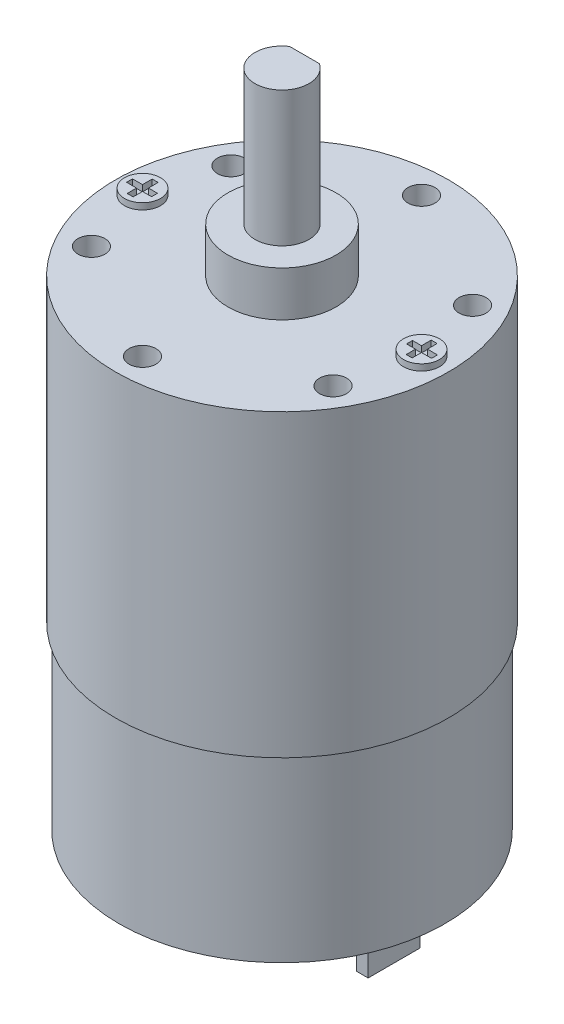
SolidWorks part; units mm, degrees
ref_plane "Front Plane" through (0, 0, 0) normal (0, 0, 1) x (1, 0, 0)
ref_plane "Top Plane" through (0, 0, 0) normal (0, 1, 0) x (1, 0, 0)
ref_plane "Right Plane" through (0, 0, 0) normal (1, 0, 0) x (0, 0, -1)
sketch "Sketch1" plane through (0, 0, 0) normal (0, 1, 0) x (1, 0, 0)
  circle A0 centre (0, 0) radius 18.1
  dimension "D1" = 36.2
extrude "Base Extrude" add sketch "Sketch1" along normal blind 20
sketch "Sketch2" plane through (0, 20, 0) normal (0, 1, 0) x (1, 0, 0)
  circle A0 centre (0, 0) radius 18.5
  dimension "D1" = 37
extrude "Motor Top" add sketch "Sketch2" along normal blind 33.3
sketch "Sketch3" plane through (0, 0, 0) normal (0, -1, 0) x (1, 0, 0)
  circle A0 centre (0, 0) radius 4.6664
extrude "Rear nub" add sketch "Sketch3" along normal blind 3.81
sketch "Sketch4" plane through (0, 0, 0) normal (0, -1, 0) x (1, 0, 0)
  line L1 (-12.7, 3.1306) -> (-11.43, 3.1306)
  line L2 (-12.7, 3.1306) -> (-12.7, -2.6581)
  line L3 (-12.7, -2.6581) -> (-11.43, -2.6581)
  line L4 (-11.43, 3.1306) -> (-11.43, -2.6581)
  line L5 (11.43, 3.1306) -> (12.7, 3.1306)
  line L6 (11.43, 3.1306) -> (11.43, -2.6581)
  line L7 (11.43, -2.6581) -> (12.7, -2.6581)
  line L8 (12.7, 3.1306) -> (12.7, -2.6581)
  dimension "D1" = 1.27
  dimension "D2" = 11.43
  dimension "D3" = 11.43
extrude "Teeth plugs" add sketch "Sketch4" along normal blind 6.35
sketch "Sketch5" plane through (0, 53.3, 0) normal (0, 1, 0) x (1, 0, 0)
  circle A0 centre (0, 0) radius 6
  dimension "D1" = 12
extrude "Axle base" add sketch "Sketch5" along normal blind 5
sketch "Sketch7" plane through (0, 58.3, 0) normal (0, 1, 0) x (1, 0, 0)
  circle A0 centre (0, 0) radius 3
  dimension "D1" = 6
extrude "Axle" add sketch "Sketch7" along normal blind 15
sketch "Sketch8" plane through (0, 0, 0) normal (1, 0, 0) x (0, 0, -1)
  line L1 (3, 73.3) -> (2.5, 73.3)
  line L2 (3, 73.3) -> (3, 59.3)
  line L3 (3, 59.3) -> (2.5, 59.3)
  line L4 (2.5, 73.3) -> (2.5, 59.3)
  point P5 (-3, 73.3)
  dimension "D1" = 5.5
  dimension "D2" = 14
extrude "D shaft cutout" cut sketch "Sketch8" against normal through all and the other way through all
sketch "Sketch9" plane through (0, 53.3, 0) normal (0, 1, 0) x (1, 0, 0)
  circle A0 centre (0, 15.5) radius 1.5
  dimension "D1" = 3
  dimension "D2" = 15.5
extrude "M3 Screw Holes" cut sketch "Sketch9" against normal blind 10
pattern_circular "Screw Hole Pattern" count 6 over 360 about axis through (0, 0, 0) along (0, 1, 0) of "M3 Screw Holes"
sketch "Sketch10" plane through (0, 53.3, 0) normal (0, 1, 0) x (1, 0, 0)
  line L0 (0, -20.35) -> (0, 20.35) construction
  line L1 (-16.9438, 0.3299) -> (-14.1667, 0.3299)
  line L2 (-16.9438, 0.3299) -> (-16.9438, -0.3299)
  line L3 (-16.9438, -0.3299) -> (-14.1667, -0.3299)
  line L4 (-14.1667, 0.3299) -> (-14.1667, -0.3299)
  line L5 (-15.8299, 1.4063) -> (-15.1701, 1.4063)
  line L6 (-15.8299, 1.4063) -> (-15.8299, -1.3707)
  line L7 (-15.8299, -1.3707) -> (-15.1701, -1.3707)
  line L8 (-15.1701, 1.4063) -> (-15.1701, -1.3707)
  line L9 (16.9438, 0.3299) -> (16.9438, -0.3299)
  line L10 (14.1667, 0.3299) -> (14.1667, -0.3299)
  line L11 (16.9438, -0.3299) -> (14.1667, -0.3299)
  line L12 (15.8299, -1.3707) -> (15.1701, -1.3707)
  line L13 (15.8299, 1.4063) -> (15.1701, 1.4063)
  line L14 (15.1701, 1.4063) -> (15.1701, -1.3707)
  line L15 (15.8299, 1.4063) -> (15.8299, -1.3707)
  line L16 (16.9438, 0.3299) -> (14.1667, 0.3299)
  circle A0 centre (-15.5, 0) radius 2
  circle A1 centre (15.5, 0) radius 2
  point P13 (-16.9438, 0)
  point P14 (-15.5, 1.4063)
  point P15 (0, 0)
  point P16 (0, 0)
  dimension "D3" = 4
  dimension "D1" = 15.5
  dimension "D2" = 15.5
extrude "Philips Screws" add sketch "Sketch10" along normal blind 0.7 contours A0 L5 L8 L1 L4 L3 L7 L6 L2 | A1 L16 L9 L11 L15 L12 L14 L10 L13
